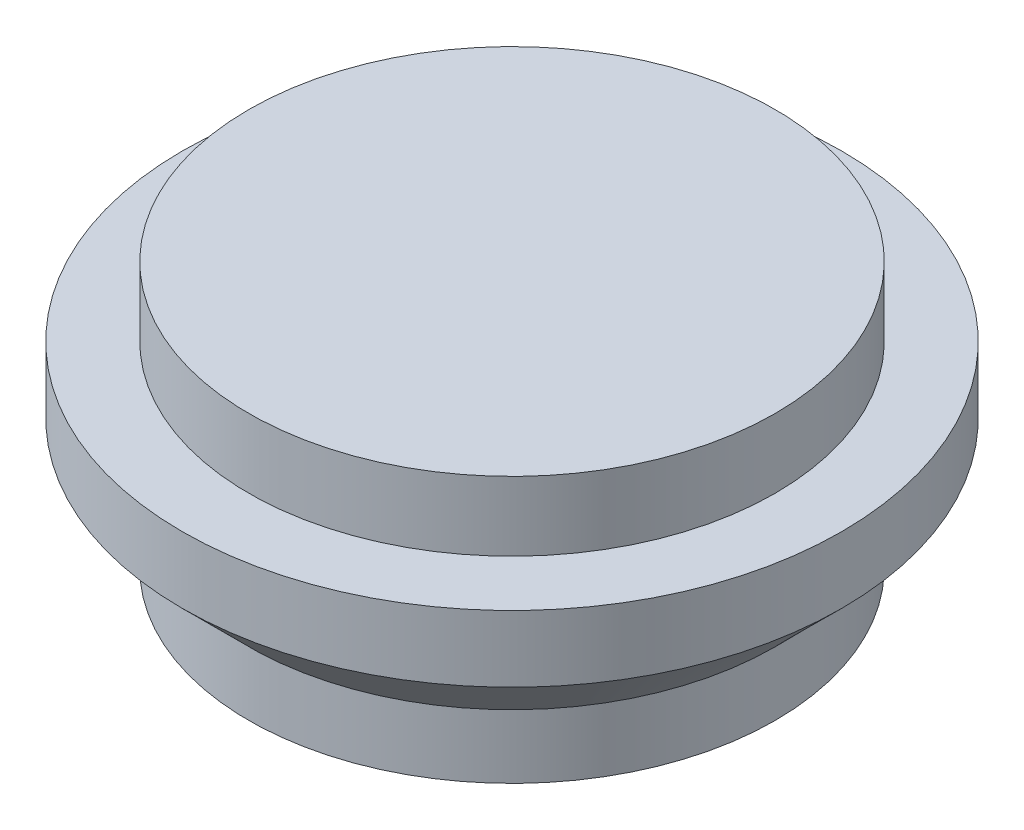
SolidWorks part; units mm, degrees
material "ABS"
ref_plane "Front Plane" through (0, 0, 0) normal (0, 0, 1) x (1, 0, 0)
ref_plane "Top Plane" through (0, 0, 0) normal (0, 1, 0) x (1, 0, 0)
ref_plane "Right Plane" through (0, 0, 0) normal (1, 0, 0) x (0, 0, -1)
sketch "Sketch2" plane through (0, 0, 0) normal (0, 0, 1) x (1, 0, 0)
  line L0 (11.303, 0) -> (12.573, 0)
  line L1 (12.573, 0) -> (12.573, 3.048)
  line L2 (12.573, 12.7) -> (0, 12.7)
  line L3 (0, 12.7) -> (0, 11.303)
  line L4 (0, 11.303) -> (11.303, 0)
  line L5 (12.573, 9.398) -> (15.748, 9.398)
  line L6 (15.748, 9.398) -> (15.748, 6.223)
  line L7 (15.748, 6.223) -> (12.573, 3.048)
  line L8 (12.573, 9.398) -> (12.573, 12.7)
  dimension "D1" = 1.27
  dimension "D2" = 12.573
  dimension "D3" = 12.7
  dimension "D4" = 45
  dimension "D5" = 3.302
  dimension "D6" = 3.175
  dimension "D7" = 3.175
  dimension "D8" = 45
revolve "Revolve1" add sketch "Sketch2" angle 360 about L3
